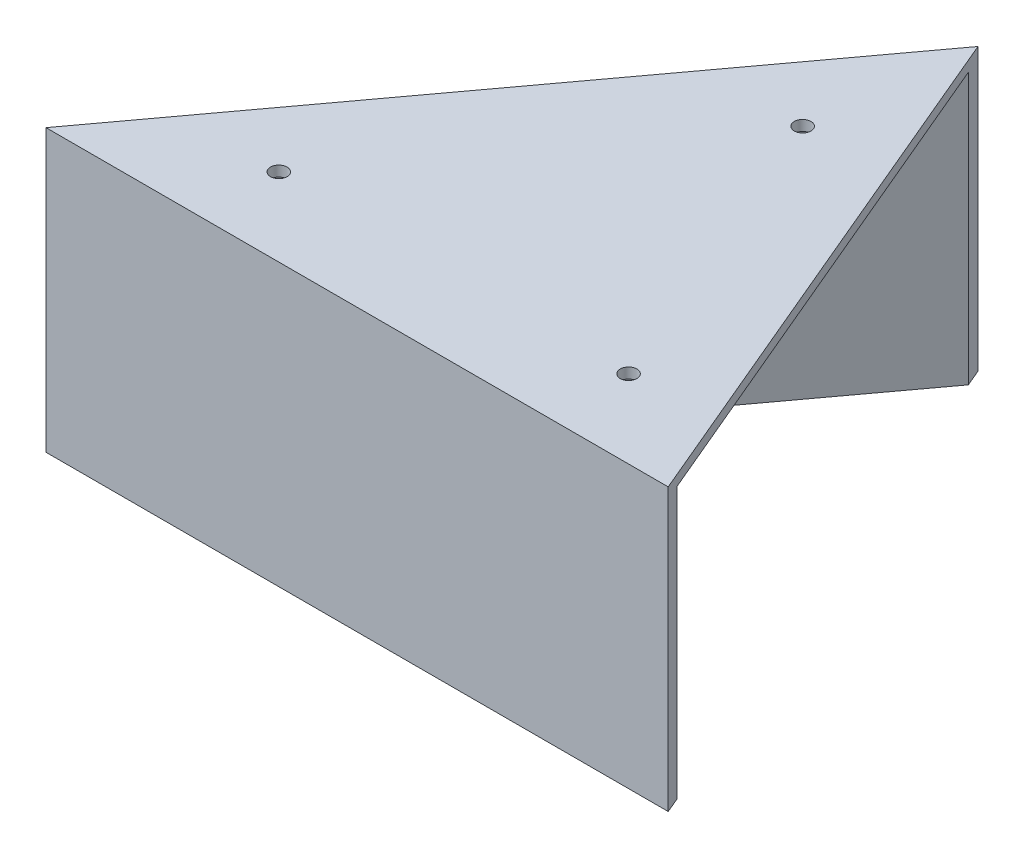
SolidWorks part; units mm, degrees
ref_plane "Front Plane" through (0, 0, 0) normal (0, 0, 1) x (1, 0, 0)
ref_plane "Top Plane" through (0, 0, 0) normal (0, 1, 0) x (1, 0, 0)
ref_plane "Right Plane" through (0, 0, 0) normal (1, 0, 0) x (0, 0, -1)
sketch "Sketch1" plane through (0, 0, 0) normal (0, 1, 0) x (1, 0, 0)
  line L1 (0, 0) -> (-69.5, 0)
  line L3 (6.5, 103) -> (-69.5, 0)
  line L4 (0, 0) -> (40, 0)
  line L6 (40, 0) -> (50, 0)
  line L7 (6.5, 103) -> (50, 0)
extrude "Boss-Extrude1" add sketch "Sketch1" along normal blind 2
sketch "Sketch2" plane through (0, 0, 0) normal (0, -1, 0) x (1, 0, 0)
  line L0 (5.786, -96.9796) -> (45.4764, -3)
  line L1 (45.4764, -3) -> (-63.5581, -3)
  line L2 (-63.5581, -3) -> (5.786, -96.9796)
  line L3 (6.5, -103) -> (50, 0)
  line L4 (50, 0) -> (-69.5, 0)
  line L5 (-69.5, 0) -> (6.5, -103)
  line L7 (50, 0) -> (-69.5, 0)
  line L8 (-69.5, 0) -> (6.5, -103)
  line L12 (6.5, -103) -> (50, 0) construction
  line L13 (6.5, -103) -> (50, 0)
  dimension "D1" = 0
  dimension "D2" = 3
extrude "Boss-Extrude2" add sketch "Sketch2" along normal blind 52
sketch "Sketch4" plane through (0, 0, 0) normal (0, -1, 0) x (1, 0, 0)
  circle A3 centre (-39.7907, -15) radius 1.6
  circle A4 centre (27.3822, -15) radius 1.6
  circle A5 centre (2.9301, -72.898) radius 1.6
extrude "Cut-Extrude3" cut sketch "Sketch4" against normal blind 52
sketch "Sketch6" plane through (0, -52, 0) normal (0, -1, 0) x (1, 0, 0)
  line L0 (5.786, -96.9796) -> (13.5663, -107.5239)
  line L1 (13.5663, -107.5239) -> (48.733, -3)
  line L2 (6.5, -103) -> (50, 0) construction
  line L3 (48.733, -3) -> (45.4764, -3)
  line L4 (45.4764, -3) -> (5.786, -96.9796)
extrude "Cut-Extrude4" cut sketch "Sketch6" against normal up to surface (52 mm away) up to face at (-39.7907, 0, -16.6)
